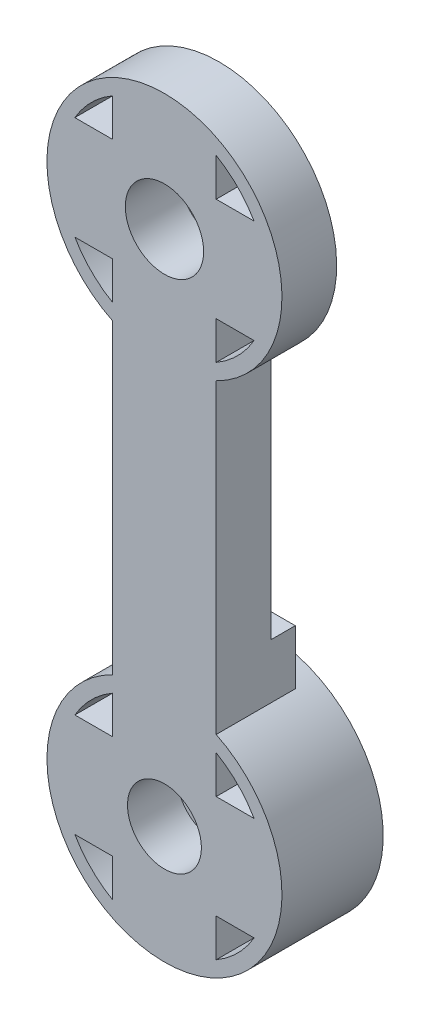
SolidWorks part; units mm, degrees
ref_plane "Front Plane" through (0, 0, 0) normal (0, 0, 1) x (1, 0, 0)
ref_plane "Top Plane" through (0, 0, 0) normal (0, 1, 0) x (1, 0, 0)
ref_plane "Right Plane" through (0, 0, 0) normal (1, 0, 0) x (0, 0, -1)
sketch "Sketch1" plane through (0, 0, 0) normal (0, 0, 1) x (1, 0, 0)
  line L5 (0, -17.5) -> (12.7696, -17.5) construction
  line L26 (0, 0) -> (0, -35) construction
  line L32 (0, 3.5) -> (7.1381, 3.5)
  line L33 (7.1381, 3.5) -> (-7.1381, 3.5)
  line L34 (0, -3.5) -> (7.1381, -3.5)
  line L35 (7.1381, -3.5) -> (-7.1381, -3.5)
  line L36 (3.5, -35) -> (3.5, -41.0622)
  line L37 (-3.5, -35) -> (-3.5, -41.0622)
  line L38 (-3.5, 0) -> (-3.5, 6.0622)
  line L45 (-3.5, 0) -> (-3.5, -35)
  line L47 (3.5, 0) -> (3.5, -35)
  line L48 (3.5, 0) -> (3.5, 6.0622)
  line L49 (7.1381, -31.5) -> (-7.1381, -31.5)
  line L50 (0, -31.5) -> (7.1381, -31.5)
  line L51 (7.1381, -38.5) -> (-7.1381, -38.5)
  line L52 (0, -38.5) -> (7.1381, -38.5)
  circle A0 centre (0, 0) radius 7.95
  circle A1 centre (0, 0) radius 3.5
  circle A2 centre (0, 0) radius 7
  circle A6 centre (0, 0) radius 1.5
  circle A11 centre (0, -35) radius 1.5
  circle A12 centre (0, -35) radius 7
  circle A13 centre (0, -35) radius 3.5
  circle A14 centre (0, -35) radius 7.95
  point P20 (0, -35)
  point P34 (0, -35)
  point P42 (0, 0)
  dimension "D1" = 15.9
  dimension "D2" = 7
  dimension "D6" = 14
  dimension "D9" = 3
  dimension "D3" = 7
  dimension "D7" = 35
extrude "Boss-Extrude4" add sketch "Sketch1" along normal blind 3 contours L48 A2 L38 L33 L32 | A2 L32 A0 L33 | L45 A14 L47 A0 | A14 L51 A12 | A12 L36 L51 L37 | A14 L49 A12 L51 | L36 A13 L51 | L51 A13 L37 | A14 L51 A12 L49 | A13 A11 | L45 A13 L49 | L49 A13 L47 | A12 L45 L49 L47 | A14 L49 A12 L45 | A14 L47 A12 L49 | A14 L45 A12 L47 | A12 L51 L37 L45 L49 | A12 L50 L47 L36 L52 | L45 A2 L47 L34 L35 | A2 L45 A0 L47 | A2 L47 A0 L34 | A2 L34 A0 L32 | A2 L33 A0 L35 | A2 L35 A0 L45 | L33 A2 L35 L45 L38 | L35 A2 L33 L48 L47 | A1 L34 L47 | A1 A6 | A1 L45 L35 | A1 L33 L38 | A1 L48 L32
sketch "Sketch3" plane through (0, 0, 0) normal (0, 0, -1) x (-1, 0, 0)
  line L0 (-3.5, 6.0622) -> (-3.5, 3.5)
  line L1 (-3.5, 3.5) -> (-6.0622, 3.5)
  line L2 (-3.5, -6.0622) -> (-3.5, -3.5)
  line L3 (-3.5, -3.5) -> (-6.0622, -3.5)
  line L4 (3.5, -6.0622) -> (3.5, -3.5)
  line L5 (3.5, -3.5) -> (6.0622, -3.5)
  line L6 (3.5, 6.0622) -> (3.5, 3.5)
  line L7 (3.5, 3.5) -> (6.0622, 3.5)
  line L8 (0, 0) -> (0, -35) construction
  line L9 (0, -35) -> (0, -17.5) construction
  line L10 (0, -17.5) -> (14.5774, -17.5) construction
  line L11 (-3.5, 3.5) -> (-6.0622, 3.5)
  line L12 (-3.5, 6.0622) -> (-3.5, 3.5)
  line L13 (-3.5, -3.5) -> (-6.0622, -3.5)
  line L14 (-3.5, -6.0622) -> (-3.5, -3.5)
  line L15 (3.5, -3.5) -> (6.0622, -3.5)
  line L16 (3.5, -6.0622) -> (3.5, -3.5)
  line L17 (3.5, 3.5) -> (6.0622, 3.5)
  line L18 (3.5, 6.0622) -> (3.5, 3.5)
  line L19 (3.5, -41.0622) -> (3.5, -38.5)
  line L20 (3.5, -38.5) -> (6.0622, -38.5)
  line L21 (3.5, -28.9378) -> (3.5, -31.5)
  line L22 (3.5, -31.5) -> (6.0622, -31.5)
  line L23 (-3.5, -28.9378) -> (-3.5, -31.5)
  line L24 (-3.5, -31.5) -> (-6.0622, -31.5)
  line L25 (-3.5, -41.0622) -> (-3.5, -38.5)
  line L26 (-3.5, -38.5) -> (-6.0622, -38.5)
  line L27 (3.5, -38.5) -> (6.0622, -38.5)
  line L28 (3.5, -41.0622) -> (3.5, -38.5)
  line L29 (3.5, -31.5) -> (6.0622, -31.5)
  line L30 (3.5, -28.9378) -> (3.5, -31.5)
  line L31 (-3.5, -31.5) -> (-6.0622, -31.5)
  line L32 (-3.5, -28.9378) -> (-3.5, -31.5)
  line L33 (-3.5, -38.5) -> (-6.0622, -38.5)
  line L34 (-3.5, -41.0622) -> (-3.5, -38.5)
  circle A0 centre (0, 0) radius 1.5
  circle A1 centre (0, 0) radius 7.95
  circle A2 centre (0, 0) radius 7
  circle A3 centre (0, -35) radius 7
  circle A4 centre (0, -35) radius 7.95
  circle A5 centre (0, -35) radius 1.5
  line M2 (3.5, -38.5) -> (6.0622, -38.5)
  arc M3 (6.0622, -38.5) -> (3.5, -41.0622) centre (0, -35) cw
  line M4 (3.5, -41.0622) -> (3.5, -38.5)
  line M5 (-3.5, -38.5) -> (-3.5, -41.0622)
  arc M6 (-3.5, -41.0622) -> (-6.0622, -38.5) centre (0, -35) cw
  line M7 (-6.0622, -38.5) -> (-3.5, -38.5)
  arc M9 (3.5, -7.1381) -> (-3.5, -7.1381) centre (0, 0) ccw
  arc M11 (-3.5, -27.8619) -> (3.5, -27.8619) centre (0, -35) ccw
  line M12 (6.0622, -31.5) -> (3.5, -31.5)
  line M13 (3.5, -31.5) -> (3.5, -28.9378)
  arc M14 (3.5, -28.9378) -> (6.0622, -31.5) centre (0, -35) cw
  arc M15 (-3.5, -6.0622) -> (-6.0622, -3.5) centre (0, 0) cw
  line M16 (-6.0622, -3.5) -> (-3.5, -3.5)
  line M17 (-3.5, -3.5) -> (-3.5, -6.0622)
  line M18 (-3.5, -31.5) -> (-6.0622, -31.5)
  arc M19 (-6.0622, -31.5) -> (-3.5, -28.9378) centre (0, -35) cw
  line M20 (-3.5, -28.9378) -> (-3.5, -31.5)
  line M21 (3.5, -3.5) -> (6.0622, -3.5)
  arc M22 (6.0622, -3.5) -> (3.5, -6.0622) centre (0, 0) cw
  line M23 (3.5, -6.0622) -> (3.5, -3.5)
  line M24 (6.0622, 3.5) -> (3.5, 3.5)
  line M25 (3.5, 3.5) -> (3.5, 6.0622)
  arc M26 (3.5, 6.0622) -> (6.0622, 3.5) centre (0, 0) cw
  arc M27 (-6.0622, 3.5) -> (-3.5, 6.0622) centre (0, 0) cw
  line M28 (-3.5, 6.0622) -> (-3.5, 3.5)
  line M29 (-3.5, 3.5) -> (-6.0622, 3.5)
  circle M30 centre (0, 0) radius 1.5
  circle M31 centre (0, -35) radius 1.5
  dimension "D1" = 15.9
extrude "Boss-Extrude5" add sketch "Sketch3" along normal blind 3 contours A1 A2 M9 M26 M22 M15 M27 | A2 M25 M28 M29 M16 M17 M23 M21 M24 M30 | A3 M4 M2 M12 M13 M20 M18 M7 M5 M31 | A4 A3 M11 M3 M6 M19 M14
sketch "Sketch4" plane through (0, 0, 3) normal (0, 0, 1) x (1, 0, 0)
  line L0 (0, 0) -> (0, -35) construction
  line L1 (0, -35) -> (0, 0) construction
  line L2 (0, -17.5) -> (19.6941, -17.5) construction
  circle A1 centre (0, -35) radius 2.5
  circle A2 centre (0, 0) radius 2.5
  dimension "D2" = 5
extrude "Cut-Extrude1" cut sketch "Sketch4" against normal blind 1.5
sketch "Sketch5" plane through (0, 0, -3) normal (0, 0, -1) x (-1, 0, 0)
  circle A0 centre (0, 0) radius 7
extrude "Cut-Extrude2" cut sketch "Sketch5" against normal blind 2
sketch "Sketch6" plane through (0, 0, -3) normal (0, 0, -1) x (-1, 0, 0)
  circle A0 centre (0, -35) radius 7.95
extrude "Cut-Extrude3" cut sketch "Sketch6" against normal blind 1
sketch "Sketch7" plane through (0, 0, 1.5) normal (0, 0, 1) x (1, 0, 0)
  circle A0 centre (0, -35) radius 2.5
extrude "Cut-Extrude4" cut sketch "Sketch7" against normal blind 1.85
sketch "Sketch8" plane through (0, 0, -3) normal (0, 0, -1) x (-1, 0, 0)
  circle A0 centre (0, 0) radius 7.95
  circle A1 centre (0, 0) radius 7
extrude "Boss-Extrude6" add sketch "Sketch8" along normal blind 0.7
sketch "Sketch9" plane through (0, 0, -2) normal (0, 0, -1) x (-1, 0, 0)
  line L0 (-3.5, -28.9378) -> (-3.5, -31.5)
  line L1 (-3.5, -31.5) -> (-6.0622, -31.5)
  line L2 (-6.0622, -38.5) -> (-3.5, -38.5)
  line L3 (-3.5, -38.5) -> (-3.5, -41.0622)
  line L4 (6.0622, -38.5) -> (3.5, -38.5)
  line L5 (3.5, -38.5) -> (3.5, -41.0622)
  line L6 (3.5, -28.9378) -> (3.5, -31.5)
  line L7 (3.5, -31.5) -> (6.0622, -31.5)
  circle A0 centre (0, -35) radius 7.95
  circle A1 centre (0, -35) radius 7
  circle A2 centre (0, -35) radius 1.5
  line M1 (6.0622, -31.5) -> (3.5, -31.5)
  line M2 (3.5, -31.5) -> (3.5, -28.9378)
  arc M3 (3.5, -28.9378) -> (6.0622, -31.5) centre (0, -35) cw
  arc M4 (-3.5, -41.0622) -> (-6.0622, -38.5) centre (0, -35) cw
  line M5 (-6.0622, -38.5) -> (-3.5, -38.5)
  line M6 (-3.5, -38.5) -> (-3.5, -41.0622)
  arc M7 (6.0622, -38.5) -> (3.5, -41.0622) centre (0, -35) cw
  line M8 (3.5, -41.0622) -> (3.5, -38.5)
  line M9 (3.5, -38.5) -> (6.0622, -38.5)
  circle M10 centre (0, -35) radius 7.95
  line M11 (-3.5, -31.5) -> (-6.0622, -31.5)
  arc M12 (-6.0622, -31.5) -> (-3.5, -28.9378) centre (0, -35) cw
  line M13 (-3.5, -28.9378) -> (-3.5, -31.5)
  circle M14 centre (0, -35) radius 1.5
extrude "Boss-Extrude8" add sketch "Sketch9" along normal blind 0.7 contours A1 M2 M13 M11 M5 M6 M8 M9 M1 M14 | A1 M10 M3 M7 M4 M12 | A0
sketch "Sketch10" plane through (0, 0, 0) normal (0, 0, -1) x (-1, 0, 0)
  line L2 (-3.5, -7.1381) -> (-3.5, -27.8619)
  line L4 (3.5, -7.1381) -> (3.5, -27.8619)
  circle A0 centre (0, 0) radius 7.95
  circle A1 centre (0, -35) radius 7.95
  line M1 (-3.5, -7.1381) -> (-3.5, -27.8619)
  arc M2 (-3.5, -27.8619) -> (3.5, -27.8619) centre (0, -35) cw
  line M3 (3.5, -27.8619) -> (3.5, -7.1381)
  arc M4 (3.5, -7.1381) -> (-3.5, -7.1381) centre (0, 0) cw
extrude "Boss-Extrude9" add sketch "Sketch10" along normal blind 0.7 contours M4 M1 M2 M3
sketch "Sketch11" plane through (3.5, 0, 0) normal (1, 0, 0) x (0, 0, -1)
  line L0 (-3, -42.95) -> (2.7, -42.95) construction
  line L1 (3.7, 7.95) -> (0.7, 7.95)
  line L2 (3.7, 7.95) -> (3.7, -7.95)
  line L3 (3.7, -7.95) -> (0.7, -7.95)
  line L4 (0.7, 7.95) -> (0.7, -7.95)
  line L5 (2.7, -27.05) -> (0.7, -27.05)
  line L6 (2.7, -27.05) -> (2.7, -42.95)
  line L7 (2.7, -42.95) -> (0.7, -42.95)
  line L8 (0.7, -27.05) -> (0.7, -42.95)
extrude "Cut-Extrude5" cut sketch "Sketch11" against normal through all both and the other way through all
sketch "Sketch12" plane through (0, 0, -0.7) normal (0, 0, -1) x (-1, 0, 0)
  line L0 (3.5, -27.8619) -> (3.5, -7.1381) construction
  line L1 (-3.5, -27.8619) -> (3.5, -27.8619)
  line L2 (-3.5, -27.8619) -> (-3.5, -24.1619)
  line L3 (-3.5, -24.1619) -> (3.5, -24.1619)
  line L4 (3.5, -27.8619) -> (3.5, -24.1619)
  circle A0 centre (0, -35) radius 7.95
  line M3 (3.5, -27.8619) -> (3.5, -7.1381)
  line M5 (-3.5, -7.1381) -> (-3.5, -27.8619)
  dimension "D1" = 3.7
extrude "Boss-Extrude10" add sketch "Sketch12" along normal blind 0.65 contours A0 L3 M3 M5
sketch "Sketch13" plane through (0, 0, -0.7) normal (0, 0, -1) x (-1, 0, 0)
  line L0 (-6.0622, -31.5) -> (-3.5, -31.5)
  line L1 (-3.5, -31.5) -> (-3.5, -28.9378)
  line L2 (3.5, -28.9378) -> (3.5, -31.5)
  line L3 (3.5, -31.5) -> (6.0622, -31.5)
  line L4 (-6.0622, -38.5) -> (-3.5, -38.5)
  line L5 (-3.5, -38.5) -> (-3.5, -41.0622)
  line L6 (6.0622, -38.5) -> (3.5, -38.5)
  line L7 (3.5, -38.5) -> (3.5, -41.0622)
  circle A0 centre (0, -35) radius 1.5
  circle A1 centre (0, -35) radius 7.95
  circle A2 centre (0, -35) radius 7
  arc M1 (-6.0622, -31.5) -> (-3.5, -28.9378) centre (0, -35) cw
  line M2 (-3.5, -28.9378) -> (-3.5, -31.5)
  line M3 (-3.5, -31.5) -> (-6.0622, -31.5)
  line M4 (3.5, -31.5) -> (3.5, -28.9378)
  arc M5 (3.5, -28.9378) -> (6.0622, -31.5) centre (0, -35) cw
  line M6 (6.0622, -31.5) -> (3.5, -31.5)
  line M7 (3.5, -38.5) -> (6.0622, -38.5)
  arc M8 (6.0622, -38.5) -> (3.5, -41.0622) centre (0, -35) cw
  line M9 (3.5, -41.0622) -> (3.5, -38.5)
  line M10 (-3.5, -38.5) -> (-3.5, -41.0622)
  arc M11 (-3.5, -41.0622) -> (-6.0622, -38.5) centre (0, -35) cw
  line M12 (-6.0622, -38.5) -> (-3.5, -38.5)
  circle M13 centre (0, -35) radius 1.5
  arc M14 (-3.5, -27.8619) -> (3.5, -27.8619) centre (0, -35) ccw
  arc M15 (3.5, -27.8619) -> (-3.5, -27.8619) centre (0, -35) ccw
extrude "Boss-Extrude11" add sketch "Sketch13" along normal blind 2.65 contours A2 M15 M14 M5 M8 M11 M1 | A2 M4 M2 M3 M12 M10 M9 M7 M6 M13
sketch "Sketch14" plane through (0, 0, 3) normal (0, 0, 1) x (1, 0, 0)
  circle A0 centre (0, 0) radius 2.65
  dimension "D1" = 5.3
extrude "Cut-Extrude6" cut sketch "Sketch14" against normal through all
sketch "Sketch15" plane through (0, 0, -3.35) normal (0, 0, -1) x (-1, 0, 0)
  line L3 (0, -35) -> (0, -37.7939) construction
  line L4 (0, -37.7939) -> (0, -35) construction
  line L5 (3.5, -28.9378) -> (3.5, -31.5)
  line L6 (3.5, -31.5) -> (6.0622, -31.5)
  line L7 (3.5, -28.9378) -> (3.5, -31.5)
  line L8 (3.5, -31.5) -> (6.0622, -31.5)
  line L9 (0, -35) -> (2.8611, -35) construction
  line L10 (3.5, -38.5) -> (6.0622, -38.5)
  line L11 (3.5, -41.0622) -> (3.5, -38.5)
  line L12 (-3.5, -28.9378) -> (-3.5, -31.5)
  line L13 (-3.5, -31.5) -> (-6.0622, -31.5)
  line L14 (-3.5, -41.0622) -> (-3.5, -38.5)
  line L15 (-3.5, -38.5) -> (-6.0622, -38.5)
  circle A0 centre (0, -35) radius 7.95
  circle A3 centre (0, -35) radius 7.95
  circle A4 centre (0, -35) radius 7.95
  arc A7 (6.0622, -38.5) -> (3.5, -41.0622) centre (0, -35) cw
  arc A8 (6.0622, -31.5) -> (3.5, -28.9378) centre (0, -35) ccw
  arc A9 (6.0622, -31.5) -> (3.5, -28.9378) centre (0, -35) ccw
  arc A10 (-6.0622, -31.5) -> (-3.5, -28.9378) centre (0, -35) cw
  arc A11 (-6.0622, -38.5) -> (-3.5, -41.0622) centre (0, -35) ccw
  circle A12 centre (0, -35) radius 1.5
  arc M6 (3.5, -28.9378) -> (6.0622, -31.5) centre (0, -35) cw
  line M7 (6.0622, -31.5) -> (3.5, -31.5)
  line M8 (3.5, -31.5) -> (3.5, -28.9378)
  arc M9 (-6.0622, -31.5) -> (-3.5, -28.9378) centre (0, -35) cw
  line M10 (-3.5, -28.9378) -> (-3.5, -31.5)
  line M11 (-3.5, -31.5) -> (-6.0622, -31.5)
  arc M12 (-3.5, -41.0622) -> (-6.0622, -38.5) centre (0, -35) cw
  line M13 (-6.0622, -38.5) -> (-3.5, -38.5)
  line M14 (-3.5, -38.5) -> (-3.5, -41.0622)
  line M15 (3.5, -38.5) -> (6.0622, -38.5)
  arc M16 (6.0622, -38.5) -> (3.5, -41.0622) centre (0, -35) cw
  line M17 (3.5, -41.0622) -> (3.5, -38.5)
  circle M18 centre (0, -35) radius 7.95
  circle M19 centre (0, -35) radius 1.5
  dimension "D1" = 0
  dimension "D2" = 0
extrude "Boss-Extrude12" add sketch "Sketch15" along normal blind 0.5 contours M18 M19 M17 M15 M16 M14 M12 M13 M11 M9 M10 M8 M6 M7
sketch "Sketch16" plane through (0, 0, -0.7) normal (0, 0, -1) x (-1, 0, 0)
  line L167 (0, 0) -> (0, -1.624) construction
  line L168 (0, -1.624) -> (0, 0) construction
  line L169 (3.5, 6.0622) -> (3.5, 3.5)
  line L170 (3.5, 3.5) -> (6.0622, 3.5)
  line L171 (3.5, 6.0622) -> (3.5, 3.5)
  line L172 (3.5, 3.5) -> (6.0622, 3.5)
  line L173 (0, 0) -> (1.3333, 0) construction
  line L174 (3.5, -3.5) -> (6.0622, -3.5)
  line L175 (3.5, -6.0622) -> (3.5, -3.5)
  line L176 (-3.5, -6.0622) -> (-3.5, -3.5)
  line L177 (-3.5, -3.5) -> (-6.0622, -3.5)
  line L178 (-3.5, 3.5) -> (-6.0622, 3.5)
  line L179 (-3.5, 6.0622) -> (-3.5, 3.5)
  circle A0 centre (0, 0) radius 7.95
  circle A1 centre (0, 0) radius 7.95
  arc A96 (6.0622, -3.5) -> (3.5, -6.0622) centre (0, 0) cw
  arc A97 (6.0622, 3.5) -> (3.5, 6.0622) centre (0, 0) ccw
  arc A98 (6.0622, 3.5) -> (3.5, 6.0622) centre (0, 0) ccw
  arc A99 (-6.0622, -3.5) -> (-3.5, -6.0622) centre (0, 0) ccw
  arc A100 (-6.0622, 3.5) -> (-3.5, 6.0622) centre (0, 0) cw
  circle A101 centre (0, 0) radius 2.55
  dimension "D1" = 0
  dimension "D2" = 0
sketch "Sketch17" plane through (0, 0, -1.35) normal (0, 0, -1) x (-1, 0, 0)
  line L1 (-3.5, -24.1619) -> (3.5, -24.1619)
  line L2 (-3.5, -24.1619) -> (-3.5, -27.8619)
  line L3 (-3.5, -27.8619) -> (3.5, -27.8619)
  line L4 (3.5, -24.1619) -> (3.5, -27.8619)
  circle A0 centre (0, -35) radius 7.95
  arc M1 (-3.5, -27.8619) -> (3.5, -27.8619) centre (0, -35) cw
  line M2 (3.5, -27.8619) -> (3.5, -24.1619)
  line M3 (3.5, -24.1619) -> (-3.5, -24.1619)
  line M4 (-3.5, -24.1619) -> (-3.5, -27.8619)
extrude "Boss-Extrude13" add sketch "Sketch17" along normal blind 1 contours M4 M1 M2 M3
